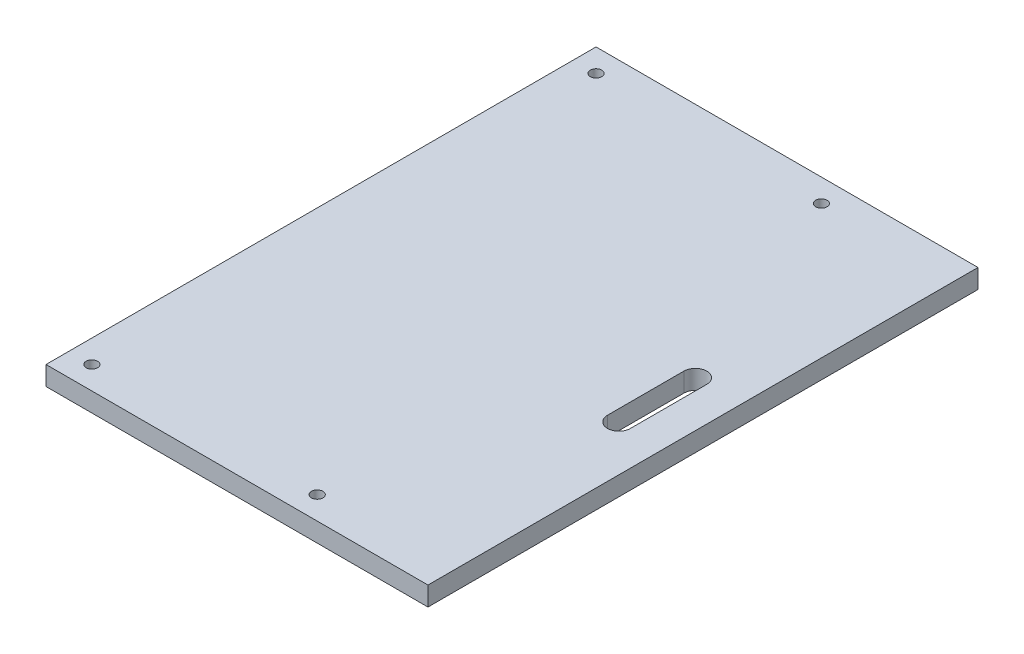
SolidWorks part; units mm, degrees
ref_plane "Front Plane" through (0, 0, 0) normal (0, 0, 1) x (1, 0, 0)
ref_plane "Top Plane" through (0, 0, 0) normal (0, 1, 0) x (1, 0, 0)
ref_plane "Right Plane" through (0, 0, 0) normal (1, 0, 0) x (0, 0, -1)
sketch "Sketch1" plane through (0, 0, 0) normal (0, 1, 0) x (1, 0, 0)
  line L0 (85, 82) -> (85, 62)
  line L1 (0, 0) -> (100, 0)
  line L2 (0, 0) -> (0, 144)
  line L3 (0, 144) -> (100, 144)
  line L4 (100, 0) -> (100, 144)
  line L5 (91, 82) -> (91, 62)
  line L6 (85, 72) -> (91, 72) construction
  arc A0 (91, 82) -> (85, 82) centre (88, 82) ccw
  arc A1 (91, 62) -> (85, 62) centre (88, 62) cw
  point P7 (0, 72)
  dimension "D3" = 3
  dimension "D1" = 144
  dimension "D2" = 100
  dimension "D4" = 10
  dimension "D5" = 12
extrude "Boss-Extrude1" add sketch "Sketch1" along normal blind 5
sketch "Sketch2" plane through (0, 5, 0) normal (0, 1, 0) x (1, 0, 0)
  line L0 (0, 144) -> (0, 0) construction
  line L1 (0, 0) -> (100, 0) construction
  line L2 (100, 144) -> (0, 144) construction
  circle A0 centre (6, 138) radius 1.5
  circle A1 centre (6, 6) radius 1.5
  circle A2 centre (65, 138) radius 1.5
  circle A3 centre (65, 6) radius 1.5
  dimension "D1" = 3
  dimension "D2" = 6
  dimension "D3" = 6
  dimension "D4" = 6
  dimension "D5" = 59
extrude "Cut-Extrude1" cut sketch "Sketch2" against normal through all
